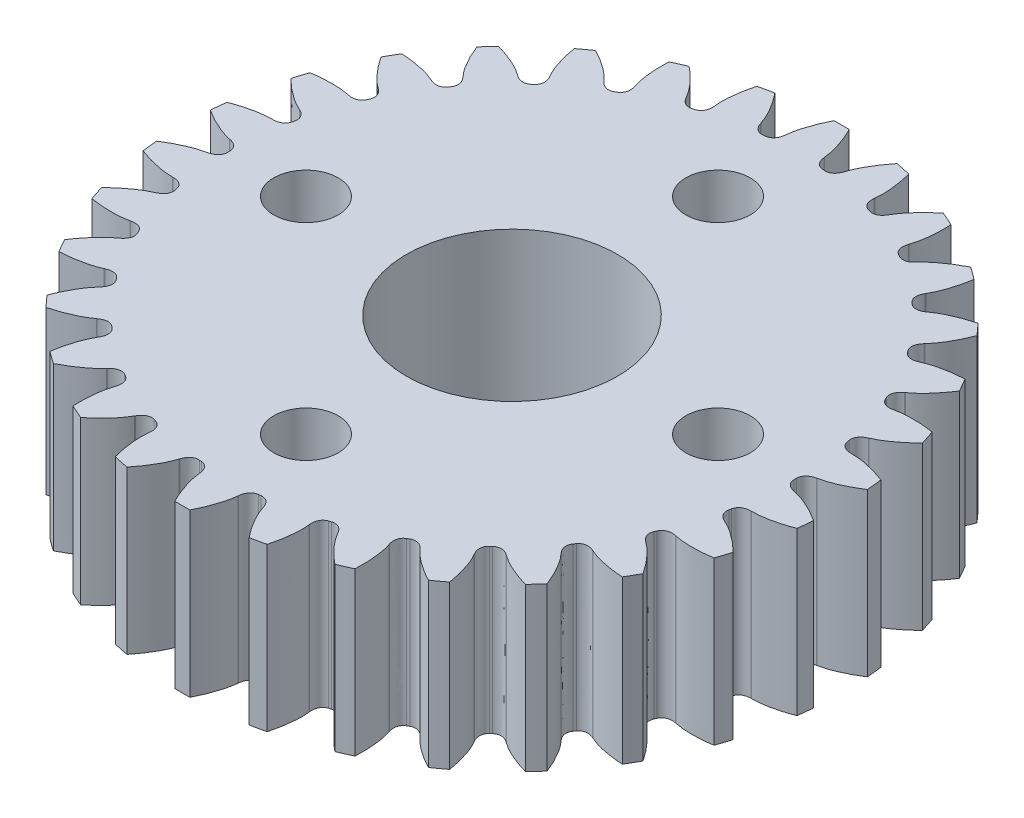
SolidWorks part; units mm, degrees
material "Stainless Steel (ferritic)"
ref_plane "Front Plane" through (0, 0, 0) normal (0, 0, 1) x (1, 0, 0)
ref_plane "Top Plane" through (0, 0, 0) normal (0, 1, 0) x (1, 0, 0)
ref_plane "Right Plane" through (0, 0, 0) normal (1, 0, 0) x (0, 0, -1)
sketch "Sketch2" plane through (0, 0, 0) normal (0, 1, 0) x (1, 0, 0)
  line L0 (11.2477, 1.9391) -> (11.2244, 1.9393)
  line L1 (11.0428, 2.7937) -> (11.064, 2.8034)
  line L2 (10.5988, 4.2353) -> (10.5759, 4.2307)
  line L3 (10.2207, 5.0286) -> (10.2394, 5.0425)
  line L4 (9.4866, 6.3463) -> (9.4652, 6.3371)
  line L5 (8.9518, 7.0437) -> (8.9672, 7.0612)
  line L6 (7.9598, 8.18) -> (7.9408, 8.1665)
  line L7 (7.2917, 8.751) -> (7.3032, 8.7712)
  line L8 (6.0851, 9.6562) -> (6.0694, 9.6391)
  line L9 (5.313, 10.0758) -> (5.32, 10.098)
  line L10 (3.9445, 10.7104) -> (3.9327, 10.6903)
  line L11 (3.102, 10.9602) -> (3.1042, 10.9834)
  line L12 (1.6315, 11.2964) -> (1.6241, 11.2744)
  line L13 (0.7555, 11.3657) -> (0.7528, 11.3888)
  line L14 (-0.7528, 11.3888) -> (-0.7555, 11.3657)
  line L15 (-1.6241, 11.2744) -> (-1.6315, 11.2964)
  line L16 (-3.1042, 10.9834) -> (-3.102, 10.9602)
  line L17 (-3.9327, 10.6903) -> (-3.9445, 10.7104)
  line L18 (-5.32, 10.098) -> (-5.313, 10.0758)
  line L19 (-6.0694, 9.6391) -> (-6.0851, 9.6562)
  line L20 (-7.3032, 8.7712) -> (-7.2917, 8.751)
  line L21 (-7.9408, 8.1665) -> (-7.9598, 8.18)
  line L22 (-8.9672, 7.0612) -> (-8.9518, 7.0437)
  line L23 (-9.4652, 6.3371) -> (-9.4866, 6.3463)
  line L24 (-10.2394, 5.0425) -> (-10.2207, 5.0286)
  line L25 (-10.5759, 4.2307) -> (-10.5988, 4.2353)
  line L26 (-11.064, 2.8034) -> (-11.0428, 2.7937)
  line L27 (-11.2244, 1.9393) -> (-11.2477, 1.9391)
  line L28 (-11.4051, 0.4418) -> (-11.3824, 0.4367)
  line L29 (-11.3824, -0.4367) -> (-11.4051, -0.4418)
  line L30 (-11.2477, -1.9391) -> (-11.2244, -1.9393)
  line L31 (-11.0428, -2.7937) -> (-11.064, -2.8034)
  line L32 (-10.5988, -4.2353) -> (-10.5759, -4.2307)
  line L33 (-10.2207, -5.0286) -> (-10.2394, -5.0425)
  line L34 (-9.4866, -6.3463) -> (-9.4652, -6.3371)
  line L35 (-8.9518, -7.0437) -> (-8.9672, -7.0612)
  line L36 (-7.9598, -8.18) -> (-7.9408, -8.1665)
  line L37 (-7.2917, -8.751) -> (-7.3032, -8.7712)
  line L38 (-6.0851, -9.6562) -> (-6.0694, -9.6391)
  line L39 (-5.313, -10.0758) -> (-5.32, -10.098)
  line L40 (-3.9445, -10.7104) -> (-3.9327, -10.6903)
  line L41 (-3.102, -10.9602) -> (-3.1042, -10.9834)
  line L42 (-1.6315, -11.2964) -> (-1.6241, -11.2744)
  line L43 (-0.7555, -11.3657) -> (-0.7528, -11.3888)
  line L44 (0.7528, -11.3888) -> (0.7555, -11.3657)
  line L45 (1.6241, -11.2744) -> (1.6315, -11.2964)
  line L46 (3.1042, -10.9834) -> (3.102, -10.9602)
  line L47 (3.9327, -10.6903) -> (3.9445, -10.7104)
  line L48 (5.32, -10.098) -> (5.313, -10.0758)
  line L49 (6.0694, -9.6391) -> (6.0851, -9.6562)
  line L50 (7.3032, -8.7712) -> (7.2917, -8.751)
  line L51 (7.9408, -8.1665) -> (7.9598, -8.18)
  line L52 (8.9672, -7.0612) -> (8.9518, -7.0437)
  line L53 (9.4652, -6.3371) -> (9.4866, -6.3463)
  line L54 (10.2394, -5.0425) -> (10.2207, -5.0286)
  line L55 (10.5759, -4.2307) -> (10.5988, -4.2353)
  line L56 (11.064, -2.8034) -> (11.0428, -2.7937)
  line L57 (11.2244, -1.9393) -> (11.2477, -1.9391)
  line L58 (11.4051, -0.4418) -> (11.3824, -0.4367)
  line L59 (11.3824, 0.4367) -> (11.4051, 0.4418)
  arc A0 (12.7573, 1.0443) -> (12.6957, 1.6309) centre (0, 0) ccw
  arc A1 (10.7693, 2.2408) -> (10.7497, 2.3332) centre (0, 0) ccw
  arc A2 (12.2614, 3.6739) -> (12.0792, 4.2349) centre (0, 0) ccw
  arc A3 (10.0681, 4.4309) -> (10.0297, 4.5172) centre (0, 0) ccw
  arc A4 (11.2296, 6.1429) -> (10.9347, 6.6537) centre (0, 0) ccw
  arc A5 (8.9268, 6.4274) -> (8.8714, 6.5038) centre (0, 0) ccw
  arc A6 (9.7071, 8.3434) -> (9.3124, 8.7818) centre (0, 0) ccw
  arc A7 (7.3954, 8.1429) -> (7.3253, 8.2061) centre (0, 0) ccw
  arc A8 (7.7603, 10.1793) -> (7.283, 10.526) centre (0, 0) ccw
  arc A9 (5.5408, 9.5026) -> (5.4591, 9.5498) centre (0, 0) ccw
  arc A10 (5.4743, 11.5703) -> (4.9354, 11.8102) centre (0, 0) ccw
  arc A11 (3.444, 10.4469) -> (3.3543, 10.4761) centre (0, 0) ccw
  arc A12 (2.9491, 12.4556) -> (2.3721, 12.5783) centre (0, 0) ccw
  arc A13 (1.1967, 10.9347) -> (1.1029, 10.9446) centre (0, 0) ccw
  arc A14 (0.2949, 12.7966) -> (-0.2949, 12.7966) centre (0, 0) ccw
  arc A15 (-1.1029, 10.9446) -> (-1.1967, 10.9347) centre (0, 0) ccw
  arc A16 (-2.3721, 12.5783) -> (-2.9491, 12.4556) centre (0, 0) ccw
  arc A17 (-3.3543, 10.4761) -> (-3.444, 10.4469) centre (0, 0) ccw
  arc A18 (-4.9354, 11.8102) -> (-5.4743, 11.5703) centre (0, 0) ccw
  arc A19 (-5.4591, 9.5498) -> (-5.5408, 9.5026) centre (0, 0) ccw
  arc A20 (-7.283, 10.526) -> (-7.7603, 10.1793) centre (0, 0) ccw
  arc A21 (-7.3253, 8.2061) -> (-7.3954, 8.1429) centre (0, 0) ccw
  arc A22 (-9.3124, 8.7818) -> (-9.7071, 8.3434) centre (0, 0) ccw
  arc A23 (-8.8714, 6.5038) -> (-8.9268, 6.4274) centre (0, 0) ccw
  arc A24 (-10.9347, 6.6537) -> (-11.2296, 6.1429) centre (0, 0) ccw
  arc A25 (-10.0297, 4.5172) -> (-10.0681, 4.4309) centre (0, 0) ccw
  arc A26 (-12.0792, 4.2349) -> (-12.2614, 3.6739) centre (0, 0) ccw
  arc A27 (-10.7497, 2.3332) -> (-10.7693, 2.2408) centre (0, 0) ccw
  arc A28 (-12.6957, 1.6309) -> (-12.7573, 1.0443) centre (0, 0) ccw
  arc A29 (-10.9999, 0.0472) -> (-10.9999, -0.0472) centre (0, 0) ccw
  arc A30 (-12.7573, -1.0443) -> (-12.6957, -1.6309) centre (0, 0) ccw
  arc A31 (-10.7693, -2.2408) -> (-10.7497, -2.3332) centre (0, 0) ccw
  arc A32 (-12.2614, -3.6739) -> (-12.0792, -4.2349) centre (0, 0) ccw
  arc A33 (-10.0681, -4.4309) -> (-10.0297, -4.5172) centre (0, 0) ccw
  arc A34 (-11.2296, -6.1429) -> (-10.9347, -6.6537) centre (0, 0) ccw
  arc A35 (-8.9268, -6.4274) -> (-8.8714, -6.5038) centre (0, 0) ccw
  arc A36 (-9.7071, -8.3434) -> (-9.3124, -8.7818) centre (0, 0) ccw
  arc A37 (-7.3954, -8.1429) -> (-7.3253, -8.2061) centre (0, 0) ccw
  arc A38 (-7.7603, -10.1793) -> (-7.283, -10.526) centre (0, 0) ccw
  arc A39 (-5.5408, -9.5026) -> (-5.4591, -9.5498) centre (0, 0) ccw
  arc A40 (-5.4743, -11.5703) -> (-4.9354, -11.8102) centre (0, 0) ccw
  arc A41 (-3.444, -10.4469) -> (-3.3543, -10.4761) centre (0, 0) ccw
  arc A42 (-2.9491, -12.4556) -> (-2.3721, -12.5783) centre (0, 0) ccw
  arc A43 (-1.1967, -10.9347) -> (-1.1029, -10.9446) centre (0, 0) ccw
  arc A44 (-0.2949, -12.7966) -> (0.2949, -12.7966) centre (0, 0) ccw
  arc A45 (1.1029, -10.9446) -> (1.1967, -10.9347) centre (0, 0) ccw
  arc A46 (2.3721, -12.5783) -> (2.9491, -12.4556) centre (0, 0) ccw
  arc A47 (3.3543, -10.4761) -> (3.444, -10.4469) centre (0, 0) ccw
  arc A48 (4.9354, -11.8102) -> (5.4743, -11.5703) centre (0, 0) ccw
  arc A49 (5.4591, -9.5498) -> (5.5408, -9.5026) centre (0, 0) ccw
  arc A50 (7.283, -10.526) -> (7.7603, -10.1793) centre (0, 0) ccw
  arc A51 (7.3253, -8.2061) -> (7.3954, -8.1429) centre (0, 0) ccw
  arc A52 (9.3124, -8.7818) -> (9.7071, -8.3434) centre (0, 0) ccw
  arc A53 (8.8714, -6.5038) -> (8.9268, -6.4274) centre (0, 0) ccw
  arc A54 (10.9347, -6.6537) -> (11.2296, -6.1429) centre (0, 0) ccw
  arc A55 (10.0297, -4.5172) -> (10.0681, -4.4309) centre (0, 0) ccw
  arc A56 (12.0792, -4.2349) -> (12.2614, -3.6739) centre (0, 0) ccw
  arc A57 (10.7497, -2.3332) -> (10.7693, -2.2408) centre (0, 0) ccw
  arc A58 (12.6957, -1.6309) -> (12.7573, -1.0443) centre (0, 0) ccw
  arc A59 (10.9999, -0.0472) -> (10.9999, 0.0472) centre (0, 0) ccw
  spline S0 degree 3 poles (11.2477, 1.9391) (11.3199, 1.9402) (11.4408, 1.9352) (11.6177, 1.9166) (11.7868, 1.8908) (11.979, 1.8522) (12.1936, 1.7985) (12.4359, 1.7256) (12.6049, 1.6656) (12.6957, 1.6309) knots 0 0 0 0 0.000217 0.000362 0.000533 0.000729 0.00095 0.001196 0.001488 0.001488 0.001488 0.001488
  spline S1 degree 3 poles (11.2244, 1.9393) (11.2014, 1.9391) (11.1629, 1.9411) (11.1089, 1.9479) (11.0618, 1.9575) (11.0126, 1.9722) (10.9605, 1.9945) (10.9048, 2.0282) (10.8236, 2.1004) (10.7817, 2.18) (10.7693, 2.2408) knots 0 0 0 0 0.000069 0.000115 0.000162 0.000212 0.000267 0.000331 0.000405 0.000589 0.000589 0.000589 0.000589
  spline S2 degree 3 poles (10.7497, 2.3332) (10.7363, 2.3938) (10.7421, 2.4836) (10.787, 2.5825) (10.8241, 2.636) (10.8627, 2.6775) (10.9016, 2.711) (10.9408, 2.7389) (10.9873, 2.767) (11.0216, 2.7846) (11.0428, 2.7937) knots 0 0 0 0 0.000185 0.000259 0.000323 0.000378 0.000429 0.000476 0.000522 0.000591 0.000591 0.000591 0.000591
  spline S3 degree 3 poles (11.064, 2.8034) (11.1304, 2.8318) (11.2388, 2.8855) (11.3928, 2.9744) (11.5368, 3.0667) (11.6968, 3.1802) (11.8709, 3.3165) (12.0626, 3.4817) (12.1926, 3.6052) (12.2614, 3.6739) knots 0 0 0 0 0.000217 0.000362 0.000533 0.000729 0.00095 0.001196 0.001488 0.001488 0.001488 0.001488
  spline S4 degree 3 poles (12.0792, 4.2349) (11.9831, 4.2499) (11.8054, 4.2735) (11.5532, 4.2944) (11.3322, 4.3023) (11.1361, 4.3001) (10.9653, 4.2902) (10.7884, 4.2715) (10.6692, 4.2513) (10.5988, 4.2353) knots 0 0 0 0 0.000292 0.000538 0.00076 0.000956 0.001127 0.001273 0.00149 0.00149 0.00149 0.00149
  spline S5 degree 3 poles (10.5759, 4.2307) (10.5534, 4.2256) (10.5153, 4.2196) (10.4612, 4.215) (10.4131, 4.2146) (10.3619, 4.2188) (10.3063, 4.2297) (10.2449, 4.2511) (10.1504, 4.3048) (10.0928, 4.374) (10.0681, 4.4309) knots 0 0 0 0 0.000069 0.000115 0.000162 0.000212 0.000267 0.000331 0.000405 0.000589 0.000589 0.000589 0.000589
  spline S6 degree 3 poles (10.0297, 4.5172) (10.004, 4.5737) (9.991, 4.6627) (10.0144, 4.7689) (10.0395, 4.8288) (10.0687, 4.8775) (10.0997, 4.9183) (10.1322, 4.9538) (10.1719, 4.991) (10.2019, 5.0152) (10.2207, 5.0286) knots 0 0 0 0 0.000185 0.000259 0.000323 0.000378 0.000429 0.000476 0.000522 0.000591 0.000591 0.000591 0.000591
  spline S7 degree 3 poles (10.2394, 5.0425) (10.2984, 5.0841) (10.3932, 5.1591) (10.5255, 5.2781) (10.6471, 5.3984) (10.7799, 5.5426) (10.922, 5.7122) (11.0752, 5.9136) (11.1766, 6.0614) (11.2296, 6.1429) knots 0 0 0 0 0.000217 0.000362 0.000533 0.000729 0.00095 0.001196 0.001488 0.001488 0.001488 0.001488
  spline S8 degree 3 poles (10.9347, 6.6537) (10.8377, 6.6485) (10.6589, 6.6346) (10.4079, 6.6026) (10.19, 6.5644) (9.9987, 6.5215) (9.8337, 6.4763) (9.6646, 6.4212) (9.5521, 6.3766) (9.4866, 6.3463) knots 0 0 0 0 0.000292 0.000538 0.00076 0.000956 0.001127 0.001273 0.00149 0.00149 0.00149 0.00149
  spline S9 degree 3 poles (9.4652, 6.3371) (9.4442, 6.3274) (9.4083, 6.3137) (9.3562, 6.2979) (9.3092, 6.2875) (9.2584, 6.281) (9.2017, 6.2801) (9.1371, 6.2883) (9.0335, 6.3211) (8.9629, 6.3769) (8.9268, 6.4274) knots 0 0 0 0 0.000069 0.000115 0.000162 0.000212 0.000267 0.000331 0.000405 0.000589 0.000589 0.000589 0.000589
  spline S10 degree 3 poles (8.8714, 6.5038) (8.8344, 6.5537) (8.8033, 6.6381) (8.804, 6.7468) (8.8162, 6.8106) (8.8345, 6.8643) (8.8565, 6.9107) (8.8809, 6.9521) (8.912, 6.9968) (8.9362, 7.0267) (8.9518, 7.0437) knots 0 0 0 0 0.000185 0.000259 0.000323 0.000378 0.000429 0.000476 0.000522 0.000591 0.000591 0.000591 0.000591
  spline S11 degree 3 poles (8.9672, 7.0612) (9.0163, 7.1141) (9.0935, 7.2073) (9.1981, 7.3511) (9.2921, 7.494) (9.392, 7.6628) (9.4957, 7.8582) (9.6036, 8.087) (9.6721, 8.2527) (9.7071, 8.3434) knots 0 0 0 0 0.000217 0.000362 0.000533 0.000729 0.00095 0.001196 0.001488 0.001488 0.001488 0.001488
  spline S12 degree 3 poles (9.3124, 8.7818) (9.2185, 8.7565) (9.0466, 8.7057) (8.8077, 8.6223) (8.6025, 8.5396) (8.4243, 8.4578) (8.2723, 8.3793) (8.1183, 8.2903) (8.0176, 8.2233) (7.9598, 8.18) knots 0 0 0 0 0.000292 0.000538 0.00076 0.000956 0.001127 0.001273 0.00149 0.00149 0.00149 0.00149
  spline S13 degree 3 poles (7.9408, 8.1665) (7.9223, 8.1527) (7.89, 8.1318) (7.8424, 8.1055) (7.7986, 8.0856) (7.7502, 8.0686) (7.6949, 8.056) (7.6301, 8.0506) (7.5219, 8.0612) (7.4412, 8.101) (7.3954, 8.1429) knots 0 0 0 0 0.000069 0.000115 0.000162 0.000212 0.000267 0.000331 0.000405 0.000589 0.000589 0.000589 0.000589
  spline S14 degree 3 poles (7.3253, 8.2061) (7.2788, 8.2472) (7.2308, 8.3233) (7.2089, 8.4298) (7.2075, 8.4948) (7.2143, 8.5511) (7.2261, 8.601) (7.2414, 8.6467) (7.2625, 8.6968) (7.28, 8.7311) (7.2917, 8.751) knots 0 0 0 0 0.000185 0.000259 0.000323 0.000378 0.000429 0.000476 0.000522 0.000591 0.000591 0.000591 0.000591
  spline S15 degree 3 poles (7.3032, 8.7712) (7.3402, 8.8333) (7.3963, 8.9404) (7.4687, 9.1029) (7.5309, 9.2622) (7.5936, 9.448) (7.6544, 9.6607) (7.7124, 9.907) (7.7449, 10.0833) (7.7603, 10.1793) knots 0 0 0 0 0.000217 0.000362 0.000533 0.000729 0.00095 0.001196 0.001488 0.001488 0.001488 0.001488
  spline S16 degree 3 poles (7.283, 10.526) (7.1965, 10.4818) (7.0389, 10.3963) (6.8225, 10.2651) (6.6391, 10.1415) (6.4817, 10.0245) (6.3494, 9.9161) (6.2173, 9.797) (6.1327, 9.7106) (6.0851, 9.6562) knots 0 0 0 0 0.000292 0.000538 0.00076 0.000956 0.001127 0.001273 0.00149 0.00149 0.00149 0.00149
  spline S17 degree 3 poles (6.0694, 9.6391) (6.0541, 9.6217) (6.0269, 9.5945) (5.9857, 9.5589) (5.9471, 9.5303) (5.9033, 9.5037) (5.8518, 9.4798) (5.7895, 9.461) (5.6815, 9.4489) (5.5943, 9.4711) (5.5408, 9.5026) knots 0 0 0 0 0.000069 0.000115 0.000162 0.000212 0.000267 0.000331 0.000405 0.000589 0.000589 0.000589 0.000589
  spline S18 degree 3 poles (5.4591, 9.5498) (5.405, 9.5804) (5.3422, 9.6448) (5.2987, 9.7444) (5.2838, 9.8077) (5.2788, 9.8642) (5.28, 9.9155) (5.2854, 9.9633) (5.2956, 10.0167) (5.3056, 10.0539) (5.313, 10.0758) knots 0 0 0 0 0.000185 0.000259 0.000323 0.000378 0.000429 0.000476 0.000522 0.000591 0.000591 0.000591 0.000591
  spline S19 degree 3 poles (5.32, 10.098) (5.3432, 10.1664) (5.3758, 10.2828) (5.4129, 10.4568) (5.4406, 10.6256) (5.4633, 10.8204) (5.4785, 11.041) (5.4841, 11.294) (5.4792, 11.4732) (5.4743, 11.5703) knots 0 0 0 0 0.000217 0.000362 0.000533 0.000729 0.00095 0.001196 0.001488 0.001488 0.001488 0.001488
  spline S20 degree 3 poles (4.9354, 11.8102) (4.86, 11.749) (4.7235, 11.6326) (4.5392, 11.4592) (4.3854, 11.3003) (4.2559, 11.1531) (4.149, 11.0195) (4.0445, 10.8756) (3.9797, 10.7734) (3.9445, 10.7104) knots 0 0 0 0 0.000292 0.000538 0.00076 0.000956 0.001127 0.001273 0.00149 0.00149 0.00149 0.00149
  spline S21 degree 3 poles (3.9327, 10.6903) (3.9214, 10.6702) (3.9004, 10.6379) (3.8675, 10.5946) (3.8356, 10.5585) (3.7983, 10.5233) (3.753, 10.4893) (3.696, 10.458) (3.5928, 10.4237) (3.5029, 10.4272) (3.444, 10.4469) knots 0 0 0 0 0.000069 0.000115 0.000162 0.000212 0.000267 0.000331 0.000405 0.000589 0.000589 0.000589 0.000589
  spline S22 degree 3 poles (3.3543, 10.4761) (3.2951, 10.4948) (3.2202, 10.5447) (3.157, 10.6331) (3.1292, 10.6919) (3.1125, 10.7462) (3.103, 10.7966) (3.0984, 10.8444) (3.0973, 10.8988) (3.0993, 10.9373) (3.102, 10.9602) knots 0 0 0 0 0.000185 0.000259 0.000323 0.000378 0.000429 0.000476 0.000522 0.000591 0.000591 0.000591 0.000591
  spline S23 degree 3 poles (3.1042, 10.9834) (3.1128, 11.0551) (3.1204, 11.1758) (3.1205, 11.3537) (3.1125, 11.5245) (3.0942, 11.7198) (3.0632, 11.9388) (3.0161, 12.1874) (2.9741, 12.3617) (2.9491, 12.4556) knots 0 0 0 0 0.000217 0.000362 0.000533 0.000729 0.00095 0.001196 0.001488 0.001488 0.001488 0.001488
  spline S24 degree 3 poles (2.3721, 12.5783) (2.311, 12.5027) (2.2017, 12.3605) (2.0575, 12.1526) (1.9402, 11.9651) (1.844, 11.7942) (1.7672, 11.6413) (1.6949, 11.4788) (1.6529, 11.3654) (1.6315, 11.2964) knots 0 0 0 0 0.000292 0.000538 0.00076 0.000956 0.001127 0.001273 0.00149 0.00149 0.00149 0.00149
  spline S25 degree 3 poles (1.6241, 11.2744) (1.6172, 11.2523) (1.6034, 11.2164) (1.5803, 11.1671) (1.5566, 11.1253) (1.5274, 11.0831) (1.4901, 11.0403) (1.4408, 10.9979) (1.3471, 10.9429) (1.2584, 10.9277) (1.1967, 10.9347) knots 0 0 0 0 0.000069 0.000115 0.000162 0.000212 0.000267 0.000331 0.000405 0.000589 0.000589 0.000589 0.000589
  spline S26 degree 3 poles (1.1029, 10.9446) (1.0411, 10.9505) (0.9575, 10.9838) (0.8772, 11.0571) (0.8379, 11.1089) (0.8103, 11.1585) (0.7905, 11.2058) (0.776, 11.2517) (0.7637, 11.3046) (0.7576, 11.3427) (0.7555, 11.3657) knots 0 0 0 0 0.000185 0.000259 0.000323 0.000378 0.000429 0.000476 0.000522 0.000591 0.000591 0.000591 0.000591
  spline S27 degree 3 poles (0.7528, 11.3888) (0.7463, 11.4607) (0.7287, 11.5804) (0.6918, 11.7544) (0.6484, 11.9198) (0.5899, 12.107) (0.5141, 12.3148) (0.4163, 12.5482) (0.3389, 12.7099) (0.2949, 12.7966) knots 0 0 0 0 0.000217 0.000362 0.000533 0.000729 0.00095 0.001196 0.001488 0.001488 0.001488 0.001488
  spline S28 degree 3 poles (-0.2949, 12.7966) (-0.3389, 12.7099) (-0.4163, 12.5482) (-0.5141, 12.3148) (-0.5899, 12.107) (-0.6484, 11.9198) (-0.6918, 11.7544) (-0.7287, 11.5804) (-0.7463, 11.4607) (-0.7528, 11.3888) knots 0 0 0 0 0.000292 0.000538 0.00076 0.000956 0.001127 0.001273 0.00149 0.00149 0.00149 0.00149
  spline S29 degree 3 poles (-0.7555, 11.3657) (-0.7576, 11.3427) (-0.7637, 11.3046) (-0.776, 11.2517) (-0.7905, 11.2058) (-0.8103, 11.1585) (-0.8379, 11.1089) (-0.8772, 11.0571) (-0.9575, 10.9838) (-1.0411, 10.9505) (-1.1029, 10.9446) knots 0 0 0 0 0.000069 0.000115 0.000162 0.000212 0.000267 0.000331 0.000405 0.000589 0.000589 0.000589 0.000589
  spline S30 degree 3 poles (-1.1967, 10.9347) (-1.2584, 10.9277) (-1.3471, 10.9429) (-1.4408, 10.9979) (-1.4901, 11.0403) (-1.5274, 11.0831) (-1.5566, 11.1253) (-1.5803, 11.1671) (-1.6034, 11.2164) (-1.6172, 11.2523) (-1.6241, 11.2744) knots 0 0 0 0 0.000185 0.000259 0.000323 0.000378 0.000429 0.000476 0.000522 0.000591 0.000591 0.000591 0.000591
  spline S31 degree 3 poles (-1.6315, 11.2964) (-1.6529, 11.3654) (-1.6949, 11.4788) (-1.7672, 11.6413) (-1.844, 11.7942) (-1.9402, 11.9651) (-2.0575, 12.1526) (-2.2017, 12.3605) (-2.311, 12.5027) (-2.3721, 12.5783) knots 0 0 0 0 0.000217 0.000362 0.000533 0.000729 0.00095 0.001196 0.001488 0.001488 0.001488 0.001488
  spline S32 degree 3 poles (-2.9491, 12.4556) (-2.9741, 12.3617) (-3.0161, 12.1874) (-3.0632, 11.9388) (-3.0942, 11.7198) (-3.1125, 11.5245) (-3.1205, 11.3537) (-3.1204, 11.1758) (-3.1128, 11.0551) (-3.1042, 10.9834) knots 0 0 0 0 0.000292 0.000538 0.00076 0.000956 0.001127 0.001273 0.00149 0.00149 0.00149 0.00149
  spline S33 degree 3 poles (-3.102, 10.9602) (-3.0993, 10.9373) (-3.0973, 10.8988) (-3.0984, 10.8444) (-3.103, 10.7966) (-3.1125, 10.7462) (-3.1292, 10.6919) (-3.157, 10.6331) (-3.2202, 10.5447) (-3.2951, 10.4948) (-3.3543, 10.4761) knots 0 0 0 0 0.000069 0.000115 0.000162 0.000212 0.000267 0.000331 0.000405 0.000589 0.000589 0.000589 0.000589
  spline S34 degree 3 poles (-3.444, 10.4469) (-3.5029, 10.4272) (-3.5928, 10.4237) (-3.696, 10.458) (-3.753, 10.4893) (-3.7983, 10.5233) (-3.8356, 10.5585) (-3.8675, 10.5946) (-3.9004, 10.6379) (-3.9214, 10.6702) (-3.9327, 10.6903) knots 0 0 0 0 0.000185 0.000259 0.000323 0.000378 0.000429 0.000476 0.000522 0.000591 0.000591 0.000591 0.000591
  spline S35 degree 3 poles (-3.9445, 10.7104) (-3.9797, 10.7734) (-4.0445, 10.8756) (-4.149, 11.0195) (-4.2559, 11.1531) (-4.3854, 11.3003) (-4.5392, 11.4592) (-4.7235, 11.6326) (-4.86, 11.749) (-4.9354, 11.8102) knots 0 0 0 0 0.000217 0.000362 0.000533 0.000729 0.00095 0.001196 0.001488 0.001488 0.001488 0.001488
  spline S36 degree 3 poles (-5.4743, 11.5703) (-5.4792, 11.4732) (-5.4841, 11.294) (-5.4785, 11.041) (-5.4633, 10.8204) (-5.4406, 10.6256) (-5.4129, 10.4568) (-5.3758, 10.2828) (-5.3432, 10.1664) (-5.32, 10.098) knots 0 0 0 0 0.000292 0.000538 0.00076 0.000956 0.001127 0.001273 0.00149 0.00149 0.00149 0.00149
  spline S37 degree 3 poles (-5.313, 10.0758) (-5.3056, 10.0539) (-5.2956, 10.0167) (-5.2854, 9.9633) (-5.28, 9.9155) (-5.2788, 9.8642) (-5.2838, 9.8077) (-5.2987, 9.7444) (-5.3422, 9.6448) (-5.405, 9.5804) (-5.4591, 9.5498) knots 0 0 0 0 0.000069 0.000115 0.000162 0.000212 0.000267 0.000331 0.000405 0.000589 0.000589 0.000589 0.000589
  spline S38 degree 3 poles (-5.5408, 9.5026) (-5.5943, 9.4711) (-5.6815, 9.4489) (-5.7895, 9.461) (-5.8518, 9.4798) (-5.9033, 9.5037) (-5.9471, 9.5303) (-5.9857, 9.5589) (-6.0269, 9.5945) (-6.0541, 9.6217) (-6.0694, 9.6391) knots 0 0 0 0 0.000185 0.000259 0.000323 0.000378 0.000429 0.000476 0.000522 0.000591 0.000591 0.000591 0.000591
  spline S39 degree 3 poles (-6.0851, 9.6562) (-6.1327, 9.7106) (-6.2173, 9.797) (-6.3494, 9.9161) (-6.4817, 10.0245) (-6.6391, 10.1415) (-6.8225, 10.2651) (-7.0389, 10.3963) (-7.1965, 10.4818) (-7.283, 10.526) knots 0 0 0 0 0.000217 0.000362 0.000533 0.000729 0.00095 0.001196 0.001488 0.001488 0.001488 0.001488
  spline S40 degree 3 poles (-7.7603, 10.1793) (-7.7449, 10.0833) (-7.7124, 9.907) (-7.6544, 9.6607) (-7.5936, 9.448) (-7.5309, 9.2622) (-7.4687, 9.1029) (-7.3963, 8.9404) (-7.3402, 8.8333) (-7.3032, 8.7712) knots 0 0 0 0 0.000292 0.000538 0.00076 0.000956 0.001127 0.001273 0.00149 0.00149 0.00149 0.00149
  spline S41 degree 3 poles (-7.2917, 8.751) (-7.28, 8.7311) (-7.2625, 8.6968) (-7.2414, 8.6467) (-7.2261, 8.601) (-7.2143, 8.5511) (-7.2075, 8.4948) (-7.2089, 8.4298) (-7.2308, 8.3233) (-7.2788, 8.2472) (-7.3253, 8.2061) knots 0 0 0 0 0.000069 0.000115 0.000162 0.000212 0.000267 0.000331 0.000405 0.000589 0.000589 0.000589 0.000589
  spline S42 degree 3 poles (-7.3954, 8.1429) (-7.4412, 8.101) (-7.5219, 8.0612) (-7.6301, 8.0506) (-7.6949, 8.056) (-7.7502, 8.0686) (-7.7986, 8.0856) (-7.8424, 8.1055) (-7.89, 8.1318) (-7.9223, 8.1527) (-7.9408, 8.1665) knots 0 0 0 0 0.000185 0.000259 0.000323 0.000378 0.000429 0.000476 0.000522 0.000591 0.000591 0.000591 0.000591
  spline S43 degree 3 poles (-7.9598, 8.18) (-8.0176, 8.2233) (-8.1183, 8.2903) (-8.2723, 8.3793) (-8.4243, 8.4578) (-8.6025, 8.5396) (-8.8077, 8.6223) (-9.0466, 8.7057) (-9.2185, 8.7565) (-9.3124, 8.7818) knots 0 0 0 0 0.000217 0.000362 0.000533 0.000729 0.00095 0.001196 0.001488 0.001488 0.001488 0.001488
  spline S44 degree 3 poles (-9.7071, 8.3434) (-9.6721, 8.2527) (-9.6036, 8.087) (-9.4957, 7.8582) (-9.392, 7.6628) (-9.2921, 7.494) (-9.1981, 7.3511) (-9.0935, 7.2073) (-9.0163, 7.1141) (-8.9672, 7.0612) knots 0 0 0 0 0.000292 0.000538 0.00076 0.000956 0.001127 0.001273 0.00149 0.00149 0.00149 0.00149
  spline S45 degree 3 poles (-8.9518, 7.0437) (-8.9362, 7.0267) (-8.912, 6.9968) (-8.8809, 6.9521) (-8.8565, 6.9107) (-8.8345, 6.8643) (-8.8162, 6.8106) (-8.804, 6.7468) (-8.8033, 6.6381) (-8.8344, 6.5537) (-8.8714, 6.5038) knots 0 0 0 0 0.000069 0.000115 0.000162 0.000212 0.000267 0.000331 0.000405 0.000589 0.000589 0.000589 0.000589
  spline S46 degree 3 poles (-8.9268, 6.4274) (-8.9629, 6.3769) (-9.0335, 6.3211) (-9.1371, 6.2883) (-9.2017, 6.2801) (-9.2584, 6.281) (-9.3092, 6.2875) (-9.3562, 6.2979) (-9.4083, 6.3137) (-9.4442, 6.3274) (-9.4652, 6.3371) knots 0 0 0 0 0.000185 0.000259 0.000323 0.000378 0.000429 0.000476 0.000522 0.000591 0.000591 0.000591 0.000591
  spline S47 degree 3 poles (-9.4866, 6.3463) (-9.5521, 6.3766) (-9.6646, 6.4212) (-9.8337, 6.4763) (-9.9987, 6.5215) (-10.19, 6.5644) (-10.4079, 6.6026) (-10.6589, 6.6346) (-10.8377, 6.6485) (-10.9347, 6.6537) knots 0 0 0 0 0.000217 0.000362 0.000533 0.000729 0.00095 0.001196 0.001488 0.001488 0.001488 0.001488
  spline S48 degree 3 poles (-11.2296, 6.1429) (-11.1766, 6.0614) (-11.0752, 5.9136) (-10.922, 5.7122) (-10.7799, 5.5426) (-10.6471, 5.3984) (-10.5255, 5.2781) (-10.3932, 5.1591) (-10.2984, 5.0841) (-10.2394, 5.0425) knots 0 0 0 0 0.000292 0.000538 0.00076 0.000956 0.001127 0.001273 0.00149 0.00149 0.00149 0.00149
  spline S49 degree 3 poles (-10.2207, 5.0286) (-10.2019, 5.0152) (-10.1719, 4.991) (-10.1322, 4.9538) (-10.0997, 4.9183) (-10.0687, 4.8775) (-10.0395, 4.8288) (-10.0144, 4.7689) (-9.991, 4.6627) (-10.004, 4.5737) (-10.0297, 4.5172) knots 0 0 0 0 0.000069 0.000115 0.000162 0.000212 0.000267 0.000331 0.000405 0.000589 0.000589 0.000589 0.000589
  spline S50 degree 3 poles (-10.0681, 4.4309) (-10.0928, 4.374) (-10.1504, 4.3048) (-10.2449, 4.2511) (-10.3063, 4.2297) (-10.3619, 4.2188) (-10.4131, 4.2146) (-10.4612, 4.215) (-10.5153, 4.2196) (-10.5534, 4.2256) (-10.5759, 4.2307) knots 0 0 0 0 0.000185 0.000259 0.000323 0.000378 0.000429 0.000476 0.000522 0.000591 0.000591 0.000591 0.000591
  spline S51 degree 3 poles (-10.5988, 4.2353) (-10.6692, 4.2513) (-10.7884, 4.2715) (-10.9653, 4.2902) (-11.1361, 4.3001) (-11.3322, 4.3023) (-11.5532, 4.2944) (-11.8054, 4.2735) (-11.9831, 4.2499) (-12.0792, 4.2349) knots 0 0 0 0 0.000217 0.000362 0.000533 0.000729 0.00095 0.001196 0.001488 0.001488 0.001488 0.001488
  spline S52 degree 3 poles (-12.2614, 3.6739) (-12.1926, 3.6052) (-12.0626, 3.4817) (-11.8709, 3.3165) (-11.6968, 3.1802) (-11.5368, 3.0667) (-11.3928, 2.9744) (-11.2388, 2.8855) (-11.1304, 2.8318) (-11.064, 2.8034) knots 0 0 0 0 0.000292 0.000538 0.00076 0.000956 0.001127 0.001273 0.00149 0.00149 0.00149 0.00149
  spline S53 degree 3 poles (-11.0428, 2.7937) (-11.0216, 2.7846) (-10.9873, 2.767) (-10.9408, 2.7389) (-10.9016, 2.711) (-10.8627, 2.6775) (-10.8241, 2.636) (-10.787, 2.5825) (-10.7421, 2.4836) (-10.7363, 2.3938) (-10.7497, 2.3332) knots 0 0 0 0 0.000069 0.000115 0.000162 0.000212 0.000267 0.000331 0.000405 0.000589 0.000589 0.000589 0.000589
  spline S54 degree 3 poles (-10.7693, 2.2408) (-10.7817, 2.18) (-10.8236, 2.1004) (-10.9048, 2.0282) (-10.9605, 1.9945) (-11.0126, 1.9722) (-11.0618, 1.9575) (-11.1089, 1.9479) (-11.1629, 1.9411) (-11.2014, 1.9391) (-11.2244, 1.9393) knots 0 0 0 0 0.000185 0.000259 0.000323 0.000378 0.000429 0.000476 0.000522 0.000591 0.000591 0.000591 0.000591
  spline S55 degree 3 poles (-11.2477, 1.9391) (-11.3199, 1.9402) (-11.4408, 1.9352) (-11.6177, 1.9166) (-11.7868, 1.8908) (-11.979, 1.8522) (-12.1936, 1.7985) (-12.4359, 1.7256) (-12.6049, 1.6656) (-12.6957, 1.6309) knots 0 0 0 0 0.000217 0.000362 0.000533 0.000729 0.00095 0.001196 0.001488 0.001488 0.001488 0.001488
  spline S56 degree 3 poles (-12.7573, 1.0443) (-12.6757, 0.9915) (-12.5229, 0.8977) (-12.3011, 0.776) (-12.1024, 0.6788) (-11.9223, 0.6011) (-11.7623, 0.5407) (-11.5931, 0.4858) (-11.4759, 0.4558) (-11.4051, 0.4418) knots 0 0 0 0 0.000292 0.000538 0.00076 0.000956 0.001127 0.001273 0.00149 0.00149 0.00149 0.00149
  spline S57 degree 3 poles (-11.3824, 0.4367) (-11.3597, 0.4322) (-11.3225, 0.4222) (-11.2711, 0.4043) (-11.227, 0.3851) (-11.182, 0.3605) (-11.1356, 0.3279) (-11.0882, 0.2834) (-11.0238, 0.1959) (-10.9993, 0.1093) (-10.9999, 0.0472) knots 0 0 0 0 0.000069 0.000115 0.000162 0.000212 0.000267 0.000331 0.000405 0.000589 0.000589 0.000589 0.000589
  spline S58 degree 3 poles (-10.9999, -0.0472) (-10.9993, -0.1093) (-11.0238, -0.1959) (-11.0882, -0.2834) (-11.1356, -0.3279) (-11.182, -0.3605) (-11.227, -0.3851) (-11.2711, -0.4043) (-11.3225, -0.4222) (-11.3597, -0.4322) (-11.3824, -0.4367) knots 0 0 0 0 0.000185 0.000259 0.000323 0.000378 0.000429 0.000476 0.000522 0.000591 0.000591 0.000591 0.000591
  spline S59 degree 3 poles (-11.4051, -0.4418) (-11.4759, -0.4558) (-11.5931, -0.4858) (-11.7623, -0.5407) (-11.9223, -0.6011) (-12.1024, -0.6788) (-12.3011, -0.776) (-12.5229, -0.8977) (-12.6757, -0.9915) (-12.7573, -1.0443) knots 0 0 0 0 0.000217 0.000362 0.000533 0.000729 0.00095 0.001196 0.001488 0.001488 0.001488 0.001488
  spline S60 degree 3 poles (-12.6957, -1.6309) (-12.6049, -1.6656) (-12.4359, -1.7256) (-12.1936, -1.7985) (-11.979, -1.8522) (-11.7868, -1.8908) (-11.6177, -1.9166) (-11.4408, -1.9352) (-11.3199, -1.9402) (-11.2477, -1.9391) knots 0 0 0 0 0.000292 0.000538 0.00076 0.000956 0.001127 0.001273 0.00149 0.00149 0.00149 0.00149
  spline S61 degree 3 poles (-11.2244, -1.9393) (-11.2014, -1.9391) (-11.1629, -1.9411) (-11.1089, -1.9479) (-11.0618, -1.9575) (-11.0126, -1.9722) (-10.9605, -1.9945) (-10.9048, -2.0282) (-10.8236, -2.1004) (-10.7817, -2.18) (-10.7693, -2.2408) knots 0 0 0 0 0.000069 0.000115 0.000162 0.000212 0.000267 0.000331 0.000405 0.000589 0.000589 0.000589 0.000589
  spline S62 degree 3 poles (-10.7497, -2.3332) (-10.7363, -2.3938) (-10.7421, -2.4836) (-10.787, -2.5825) (-10.8241, -2.636) (-10.8627, -2.6775) (-10.9016, -2.711) (-10.9408, -2.7389) (-10.9873, -2.767) (-11.0216, -2.7846) (-11.0428, -2.7937) knots 0 0 0 0 0.000185 0.000259 0.000323 0.000378 0.000429 0.000476 0.000522 0.000591 0.000591 0.000591 0.000591
  spline S63 degree 3 poles (-11.064, -2.8034) (-11.1304, -2.8318) (-11.2388, -2.8855) (-11.3928, -2.9744) (-11.5368, -3.0667) (-11.6968, -3.1802) (-11.8709, -3.3165) (-12.0626, -3.4817) (-12.1926, -3.6052) (-12.2614, -3.6739) knots 0 0 0 0 0.000217 0.000362 0.000533 0.000729 0.00095 0.001196 0.001488 0.001488 0.001488 0.001488
  spline S64 degree 3 poles (-12.0792, -4.2349) (-11.9831, -4.2499) (-11.8054, -4.2735) (-11.5532, -4.2944) (-11.3322, -4.3023) (-11.1361, -4.3001) (-10.9653, -4.2902) (-10.7884, -4.2715) (-10.6692, -4.2513) (-10.5988, -4.2353) knots 0 0 0 0 0.000292 0.000538 0.00076 0.000956 0.001127 0.001273 0.00149 0.00149 0.00149 0.00149
  spline S65 degree 3 poles (-10.5759, -4.2307) (-10.5534, -4.2256) (-10.5153, -4.2196) (-10.4612, -4.215) (-10.4131, -4.2146) (-10.3619, -4.2188) (-10.3063, -4.2297) (-10.2449, -4.2511) (-10.1504, -4.3048) (-10.0928, -4.374) (-10.0681, -4.4309) knots 0 0 0 0 0.000069 0.000115 0.000162 0.000212 0.000267 0.000331 0.000405 0.000589 0.000589 0.000589 0.000589
  spline S66 degree 3 poles (-10.0297, -4.5172) (-10.004, -4.5737) (-9.991, -4.6627) (-10.0144, -4.7689) (-10.0395, -4.8288) (-10.0687, -4.8775) (-10.0997, -4.9183) (-10.1322, -4.9538) (-10.1719, -4.991) (-10.2019, -5.0152) (-10.2207, -5.0286) knots 0 0 0 0 0.000185 0.000259 0.000323 0.000378 0.000429 0.000476 0.000522 0.000591 0.000591 0.000591 0.000591
  spline S67 degree 3 poles (-10.2394, -5.0425) (-10.2984, -5.0841) (-10.3932, -5.1591) (-10.5255, -5.2781) (-10.6471, -5.3984) (-10.7799, -5.5426) (-10.922, -5.7122) (-11.0752, -5.9136) (-11.1766, -6.0614) (-11.2296, -6.1429) knots 0 0 0 0 0.000217 0.000362 0.000533 0.000729 0.00095 0.001196 0.001488 0.001488 0.001488 0.001488
  spline S68 degree 3 poles (-10.9347, -6.6537) (-10.8377, -6.6485) (-10.6589, -6.6346) (-10.4079, -6.6026) (-10.19, -6.5644) (-9.9987, -6.5215) (-9.8337, -6.4763) (-9.6646, -6.4212) (-9.5521, -6.3766) (-9.4866, -6.3463) knots 0 0 0 0 0.000292 0.000538 0.00076 0.000956 0.001127 0.001273 0.00149 0.00149 0.00149 0.00149
  spline S69 degree 3 poles (-9.4652, -6.3371) (-9.4442, -6.3274) (-9.4083, -6.3137) (-9.3562, -6.2979) (-9.3092, -6.2875) (-9.2584, -6.281) (-9.2017, -6.2801) (-9.1371, -6.2883) (-9.0335, -6.3211) (-8.9629, -6.3769) (-8.9268, -6.4274) knots 0 0 0 0 0.000069 0.000115 0.000162 0.000212 0.000267 0.000331 0.000405 0.000589 0.000589 0.000589 0.000589
  spline S70 degree 3 poles (-8.8714, -6.5038) (-8.8344, -6.5537) (-8.8033, -6.6381) (-8.804, -6.7468) (-8.8162, -6.8106) (-8.8345, -6.8643) (-8.8565, -6.9107) (-8.8809, -6.9521) (-8.912, -6.9968) (-8.9362, -7.0267) (-8.9518, -7.0437) knots 0 0 0 0 0.000185 0.000259 0.000323 0.000378 0.000429 0.000476 0.000522 0.000591 0.000591 0.000591 0.000591
  spline S71 degree 3 poles (-8.9672, -7.0612) (-9.0163, -7.1141) (-9.0935, -7.2073) (-9.1981, -7.3511) (-9.2921, -7.494) (-9.392, -7.6628) (-9.4957, -7.8582) (-9.6036, -8.087) (-9.6721, -8.2527) (-9.7071, -8.3434) knots 0 0 0 0 0.000217 0.000362 0.000533 0.000729 0.00095 0.001196 0.001488 0.001488 0.001488 0.001488
  spline S72 degree 3 poles (-9.3124, -8.7818) (-9.2185, -8.7565) (-9.0466, -8.7057) (-8.8077, -8.6223) (-8.6025, -8.5396) (-8.4243, -8.4578) (-8.2723, -8.3793) (-8.1183, -8.2903) (-8.0176, -8.2233) (-7.9598, -8.18) knots 0 0 0 0 0.000292 0.000538 0.00076 0.000956 0.001127 0.001273 0.00149 0.00149 0.00149 0.00149
  spline S73 degree 3 poles (-7.9408, -8.1665) (-7.9223, -8.1527) (-7.89, -8.1318) (-7.8424, -8.1055) (-7.7986, -8.0856) (-7.7502, -8.0686) (-7.6949, -8.056) (-7.6301, -8.0506) (-7.5219, -8.0612) (-7.4412, -8.101) (-7.3954, -8.1429) knots 0 0 0 0 0.000069 0.000115 0.000162 0.000212 0.000267 0.000331 0.000405 0.000589 0.000589 0.000589 0.000589
  spline S74 degree 3 poles (-7.3253, -8.2061) (-7.2788, -8.2472) (-7.2308, -8.3233) (-7.2089, -8.4298) (-7.2075, -8.4948) (-7.2143, -8.5511) (-7.2261, -8.601) (-7.2414, -8.6467) (-7.2625, -8.6968) (-7.28, -8.7311) (-7.2917, -8.751) knots 0 0 0 0 0.000185 0.000259 0.000323 0.000378 0.000429 0.000476 0.000522 0.000591 0.000591 0.000591 0.000591
  spline S75 degree 3 poles (-7.3032, -8.7712) (-7.3402, -8.8333) (-7.3963, -8.9404) (-7.4687, -9.1029) (-7.5309, -9.2622) (-7.5936, -9.448) (-7.6544, -9.6607) (-7.7124, -9.907) (-7.7449, -10.0833) (-7.7603, -10.1793) knots 0 0 0 0 0.000217 0.000362 0.000533 0.000729 0.00095 0.001196 0.001488 0.001488 0.001488 0.001488
  spline S76 degree 3 poles (-7.283, -10.526) (-7.1965, -10.4818) (-7.0389, -10.3963) (-6.8225, -10.2651) (-6.6391, -10.1415) (-6.4817, -10.0245) (-6.3494, -9.9161) (-6.2173, -9.797) (-6.1327, -9.7106) (-6.0851, -9.6562) knots 0 0 0 0 0.000292 0.000538 0.00076 0.000956 0.001127 0.001273 0.00149 0.00149 0.00149 0.00149
  spline S77 degree 3 poles (-6.0694, -9.6391) (-6.0541, -9.6217) (-6.0269, -9.5945) (-5.9857, -9.5589) (-5.9471, -9.5303) (-5.9033, -9.5037) (-5.8518, -9.4798) (-5.7895, -9.461) (-5.6815, -9.4489) (-5.5943, -9.4711) (-5.5408, -9.5026) knots 0 0 0 0 0.000069 0.000115 0.000162 0.000212 0.000267 0.000331 0.000405 0.000589 0.000589 0.000589 0.000589
  spline S78 degree 3 poles (-5.4591, -9.5498) (-5.405, -9.5804) (-5.3422, -9.6448) (-5.2987, -9.7444) (-5.2838, -9.8077) (-5.2788, -9.8642) (-5.28, -9.9155) (-5.2854, -9.9633) (-5.2956, -10.0167) (-5.3056, -10.0539) (-5.313, -10.0758) knots 0 0 0 0 0.000185 0.000259 0.000323 0.000378 0.000429 0.000476 0.000522 0.000591 0.000591 0.000591 0.000591
  spline S79 degree 3 poles (-5.32, -10.098) (-5.3432, -10.1664) (-5.3758, -10.2828) (-5.4129, -10.4568) (-5.4406, -10.6256) (-5.4633, -10.8204) (-5.4785, -11.041) (-5.4841, -11.294) (-5.4792, -11.4732) (-5.4743, -11.5703) knots 0 0 0 0 0.000217 0.000362 0.000533 0.000729 0.00095 0.001196 0.001488 0.001488 0.001488 0.001488
  spline S80 degree 3 poles (-4.9354, -11.8102) (-4.86, -11.749) (-4.7235, -11.6326) (-4.5392, -11.4592) (-4.3854, -11.3003) (-4.2559, -11.1531) (-4.149, -11.0195) (-4.0445, -10.8756) (-3.9797, -10.7734) (-3.9445, -10.7104) knots 0 0 0 0 0.000292 0.000538 0.00076 0.000956 0.001127 0.001273 0.00149 0.00149 0.00149 0.00149
  spline S81 degree 3 poles (-3.9327, -10.6903) (-3.9214, -10.6702) (-3.9004, -10.6379) (-3.8675, -10.5946) (-3.8356, -10.5585) (-3.7983, -10.5233) (-3.753, -10.4893) (-3.696, -10.458) (-3.5928, -10.4237) (-3.5029, -10.4272) (-3.444, -10.4469) knots 0 0 0 0 0.000069 0.000115 0.000162 0.000212 0.000267 0.000331 0.000405 0.000589 0.000589 0.000589 0.000589
  spline S82 degree 3 poles (-3.3543, -10.4761) (-3.2951, -10.4948) (-3.2202, -10.5447) (-3.157, -10.6331) (-3.1292, -10.6919) (-3.1125, -10.7462) (-3.103, -10.7966) (-3.0984, -10.8444) (-3.0973, -10.8988) (-3.0993, -10.9373) (-3.102, -10.9602) knots 0 0 0 0 0.000185 0.000259 0.000323 0.000378 0.000429 0.000476 0.000522 0.000591 0.000591 0.000591 0.000591
  spline S83 degree 3 poles (-3.1042, -10.9834) (-3.1128, -11.0551) (-3.1204, -11.1758) (-3.1205, -11.3537) (-3.1125, -11.5245) (-3.0942, -11.7198) (-3.0632, -11.9388) (-3.0161, -12.1874) (-2.9741, -12.3617) (-2.9491, -12.4556) knots 0 0 0 0 0.000217 0.000362 0.000533 0.000729 0.00095 0.001196 0.001488 0.001488 0.001488 0.001488
  spline S84 degree 3 poles (-2.3721, -12.5783) (-2.311, -12.5027) (-2.2017, -12.3605) (-2.0575, -12.1526) (-1.9402, -11.9651) (-1.844, -11.7942) (-1.7672, -11.6413) (-1.6949, -11.4788) (-1.6529, -11.3654) (-1.6315, -11.2964) knots 0 0 0 0 0.000292 0.000538 0.00076 0.000956 0.001127 0.001273 0.00149 0.00149 0.00149 0.00149
  spline S85 degree 3 poles (-1.6241, -11.2744) (-1.6172, -11.2523) (-1.6034, -11.2164) (-1.5803, -11.1671) (-1.5566, -11.1253) (-1.5274, -11.0831) (-1.4901, -11.0403) (-1.4408, -10.9979) (-1.3471, -10.9429) (-1.2584, -10.9277) (-1.1967, -10.9347) knots 0 0 0 0 0.000069 0.000115 0.000162 0.000212 0.000267 0.000331 0.000405 0.000589 0.000589 0.000589 0.000589
  spline S86 degree 3 poles (-1.1029, -10.9446) (-1.0411, -10.9505) (-0.9575, -10.9838) (-0.8772, -11.0571) (-0.8379, -11.1089) (-0.8103, -11.1585) (-0.7905, -11.2058) (-0.776, -11.2517) (-0.7637, -11.3046) (-0.7576, -11.3427) (-0.7555, -11.3657) knots 0 0 0 0 0.000185 0.000259 0.000323 0.000378 0.000429 0.000476 0.000522 0.000591 0.000591 0.000591 0.000591
  spline S87 degree 3 poles (-0.7528, -11.3888) (-0.7463, -11.4607) (-0.7287, -11.5804) (-0.6918, -11.7544) (-0.6484, -11.9198) (-0.5899, -12.107) (-0.5141, -12.3148) (-0.4163, -12.5482) (-0.3389, -12.7099) (-0.2949, -12.7966) knots 0 0 0 0 0.000217 0.000362 0.000533 0.000729 0.00095 0.001196 0.001488 0.001488 0.001488 0.001488
  spline S88 degree 3 poles (0.2949, -12.7966) (0.3389, -12.7099) (0.4163, -12.5482) (0.5141, -12.3148) (0.5899, -12.107) (0.6484, -11.9198) (0.6918, -11.7544) (0.7287, -11.5804) (0.7463, -11.4607) (0.7528, -11.3888) knots 0 0 0 0 0.000292 0.000538 0.00076 0.000956 0.001127 0.001273 0.00149 0.00149 0.00149 0.00149
  spline S89 degree 3 poles (0.7555, -11.3657) (0.7576, -11.3427) (0.7637, -11.3046) (0.776, -11.2517) (0.7905, -11.2058) (0.8103, -11.1585) (0.8379, -11.1089) (0.8772, -11.0571) (0.9575, -10.9838) (1.0411, -10.9505) (1.1029, -10.9446) knots 0 0 0 0 0.000069 0.000115 0.000162 0.000212 0.000267 0.000331 0.000405 0.000589 0.000589 0.000589 0.000589
  spline S90 degree 3 poles (1.1967, -10.9347) (1.2584, -10.9277) (1.3471, -10.9429) (1.4408, -10.9979) (1.4901, -11.0403) (1.5274, -11.0831) (1.5566, -11.1253) (1.5803, -11.1671) (1.6034, -11.2164) (1.6172, -11.2523) (1.6241, -11.2744) knots 0 0 0 0 0.000185 0.000259 0.000323 0.000378 0.000429 0.000476 0.000522 0.000591 0.000591 0.000591 0.000591
  spline S91 degree 3 poles (1.6315, -11.2964) (1.6529, -11.3654) (1.6949, -11.4788) (1.7672, -11.6413) (1.844, -11.7942) (1.9402, -11.9651) (2.0575, -12.1526) (2.2017, -12.3605) (2.311, -12.5027) (2.3721, -12.5783) knots 0 0 0 0 0.000217 0.000362 0.000533 0.000729 0.00095 0.001196 0.001488 0.001488 0.001488 0.001488
  spline S92 degree 3 poles (2.9491, -12.4556) (2.9741, -12.3617) (3.0161, -12.1874) (3.0632, -11.9388) (3.0942, -11.7198) (3.1125, -11.5245) (3.1205, -11.3537) (3.1204, -11.1758) (3.1128, -11.0551) (3.1042, -10.9834) knots 0 0 0 0 0.000292 0.000538 0.00076 0.000956 0.001127 0.001273 0.00149 0.00149 0.00149 0.00149
  spline S93 degree 3 poles (3.102, -10.9602) (3.0993, -10.9373) (3.0973, -10.8988) (3.0984, -10.8444) (3.103, -10.7966) (3.1125, -10.7462) (3.1292, -10.6919) (3.157, -10.6331) (3.2202, -10.5447) (3.2951, -10.4948) (3.3543, -10.4761) knots 0 0 0 0 0.000069 0.000115 0.000162 0.000212 0.000267 0.000331 0.000405 0.000589 0.000589 0.000589 0.000589
  spline S94 degree 3 poles (3.444, -10.4469) (3.5029, -10.4272) (3.5928, -10.4237) (3.696, -10.458) (3.753, -10.4893) (3.7983, -10.5233) (3.8356, -10.5585) (3.8675, -10.5946) (3.9004, -10.6379) (3.9214, -10.6702) (3.9327, -10.6903) knots 0 0 0 0 0.000185 0.000259 0.000323 0.000378 0.000429 0.000476 0.000522 0.000591 0.000591 0.000591 0.000591
  spline S95 degree 3 poles (3.9445, -10.7104) (3.9797, -10.7734) (4.0445, -10.8756) (4.149, -11.0195) (4.2559, -11.1531) (4.3854, -11.3003) (4.5392, -11.4592) (4.7235, -11.6326) (4.86, -11.749) (4.9354, -11.8102) knots 0 0 0 0 0.000217 0.000362 0.000533 0.000729 0.00095 0.001196 0.001488 0.001488 0.001488 0.001488
  spline S96 degree 3 poles (5.4743, -11.5703) (5.4792, -11.4732) (5.4841, -11.294) (5.4785, -11.041) (5.4633, -10.8204) (5.4406, -10.6256) (5.4129, -10.4568) (5.3758, -10.2828) (5.3432, -10.1664) (5.32, -10.098) knots 0 0 0 0 0.000292 0.000538 0.00076 0.000956 0.001127 0.001273 0.00149 0.00149 0.00149 0.00149
  spline S97 degree 3 poles (5.313, -10.0758) (5.3056, -10.0539) (5.2956, -10.0167) (5.2854, -9.9633) (5.28, -9.9155) (5.2788, -9.8642) (5.2838, -9.8077) (5.2987, -9.7444) (5.3422, -9.6448) (5.405, -9.5804) (5.4591, -9.5498) knots 0 0 0 0 0.000069 0.000115 0.000162 0.000212 0.000267 0.000331 0.000405 0.000589 0.000589 0.000589 0.000589
  spline S98 degree 3 poles (5.5408, -9.5026) (5.5943, -9.4711) (5.6815, -9.4489) (5.7895, -9.461) (5.8518, -9.4798) (5.9033, -9.5037) (5.9471, -9.5303) (5.9857, -9.5589) (6.0269, -9.5945) (6.0541, -9.6217) (6.0694, -9.6391) knots 0 0 0 0 0.000185 0.000259 0.000323 0.000378 0.000429 0.000476 0.000522 0.000591 0.000591 0.000591 0.000591
  spline S99 degree 3 poles (6.0851, -9.6562) (6.1327, -9.7106) (6.2173, -9.797) (6.3494, -9.9161) (6.4817, -10.0245) (6.6391, -10.1415) (6.8225, -10.2651) (7.0389, -10.3963) (7.1965, -10.4818) (7.283, -10.526) knots 0 0 0 0 0.000217 0.000362 0.000533 0.000729 0.00095 0.001196 0.001488 0.001488 0.001488 0.001488
  spline S100 degree 3 poles (7.7603, -10.1793) (7.7449, -10.0833) (7.7124, -9.907) (7.6544, -9.6607) (7.5936, -9.448) (7.5309, -9.2622) (7.4687, -9.1029) (7.3963, -8.9404) (7.3402, -8.8333) (7.3032, -8.7712) knots 0 0 0 0 0.000292 0.000538 0.00076 0.000956 0.001127 0.001273 0.00149 0.00149 0.00149 0.00149
  spline S101 degree 3 poles (7.2917, -8.751) (7.28, -8.7311) (7.2625, -8.6968) (7.2414, -8.6467) (7.2261, -8.601) (7.2143, -8.5511) (7.2075, -8.4948) (7.2089, -8.4298) (7.2308, -8.3233) (7.2788, -8.2472) (7.3253, -8.2061) knots 0 0 0 0 0.000069 0.000115 0.000162 0.000212 0.000267 0.000331 0.000405 0.000589 0.000589 0.000589 0.000589
  spline S102 degree 3 poles (7.3954, -8.1429) (7.4412, -8.101) (7.5219, -8.0612) (7.6301, -8.0506) (7.6949, -8.056) (7.7502, -8.0686) (7.7986, -8.0856) (7.8424, -8.1055) (7.89, -8.1318) (7.9223, -8.1527) (7.9408, -8.1665) knots 0 0 0 0 0.000185 0.000259 0.000323 0.000378 0.000429 0.000476 0.000522 0.000591 0.000591 0.000591 0.000591
  spline S103 degree 3 poles (7.9598, -8.18) (8.0176, -8.2233) (8.1183, -8.2903) (8.2723, -8.3793) (8.4243, -8.4578) (8.6025, -8.5396) (8.8077, -8.6223) (9.0466, -8.7057) (9.2185, -8.7565) (9.3124, -8.7818) knots 0 0 0 0 0.000217 0.000362 0.000533 0.000729 0.00095 0.001196 0.001488 0.001488 0.001488 0.001488
  spline S104 degree 3 poles (9.7071, -8.3434) (9.6721, -8.2527) (9.6036, -8.087) (9.4957, -7.8582) (9.392, -7.6628) (9.2921, -7.494) (9.1981, -7.3511) (9.0935, -7.2073) (9.0163, -7.1141) (8.9672, -7.0612) knots 0 0 0 0 0.000292 0.000538 0.00076 0.000956 0.001127 0.001273 0.00149 0.00149 0.00149 0.00149
  spline S105 degree 3 poles (8.9518, -7.0437) (8.9362, -7.0267) (8.912, -6.9968) (8.8809, -6.9521) (8.8565, -6.9107) (8.8345, -6.8643) (8.8162, -6.8106) (8.804, -6.7468) (8.8033, -6.6381) (8.8344, -6.5537) (8.8714, -6.5038) knots 0 0 0 0 0.000069 0.000115 0.000162 0.000212 0.000267 0.000331 0.000405 0.000589 0.000589 0.000589 0.000589
  spline S106 degree 3 poles (8.9268, -6.4274) (8.9629, -6.3769) (9.0335, -6.3211) (9.1371, -6.2883) (9.2017, -6.2801) (9.2584, -6.281) (9.3092, -6.2875) (9.3562, -6.2979) (9.4083, -6.3137) (9.4442, -6.3274) (9.4652, -6.3371) knots 0 0 0 0 0.000185 0.000259 0.000323 0.000378 0.000429 0.000476 0.000522 0.000591 0.000591 0.000591 0.000591
  spline S107 degree 3 poles (9.4866, -6.3463) (9.5521, -6.3766) (9.6646, -6.4212) (9.8337, -6.4763) (9.9987, -6.5215) (10.19, -6.5644) (10.4079, -6.6026) (10.6589, -6.6346) (10.8377, -6.6485) (10.9347, -6.6537) knots 0 0 0 0 0.000217 0.000362 0.000533 0.000729 0.00095 0.001196 0.001488 0.001488 0.001488 0.001488
  spline S108 degree 3 poles (11.2296, -6.1429) (11.1766, -6.0614) (11.0752, -5.9136) (10.922, -5.7122) (10.7799, -5.5426) (10.6471, -5.3984) (10.5255, -5.2781) (10.3932, -5.1591) (10.2984, -5.0841) (10.2394, -5.0425) knots 0 0 0 0 0.000292 0.000538 0.00076 0.000956 0.001127 0.001273 0.00149 0.00149 0.00149 0.00149
  spline S109 degree 3 poles (10.2207, -5.0286) (10.2019, -5.0152) (10.1719, -4.991) (10.1322, -4.9538) (10.0997, -4.9183) (10.0687, -4.8775) (10.0395, -4.8288) (10.0144, -4.7689) (9.991, -4.6627) (10.004, -4.5737) (10.0297, -4.5172) knots 0 0 0 0 0.000069 0.000115 0.000162 0.000212 0.000267 0.000331 0.000405 0.000589 0.000589 0.000589 0.000589
  spline S110 degree 3 poles (10.0681, -4.4309) (10.0928, -4.374) (10.1504, -4.3048) (10.2449, -4.2511) (10.3063, -4.2297) (10.3619, -4.2188) (10.4131, -4.2146) (10.4612, -4.215) (10.5153, -4.2196) (10.5534, -4.2256) (10.5759, -4.2307) knots 0 0 0 0 0.000185 0.000259 0.000323 0.000378 0.000429 0.000476 0.000522 0.000591 0.000591 0.000591 0.000591
  spline S111 degree 3 poles (10.5988, -4.2353) (10.6692, -4.2513) (10.7884, -4.2715) (10.9653, -4.2902) (11.1361, -4.3001) (11.3322, -4.3023) (11.5532, -4.2944) (11.8054, -4.2735) (11.9831, -4.2499) (12.0792, -4.2349) knots 0 0 0 0 0.000217 0.000362 0.000533 0.000729 0.00095 0.001196 0.001488 0.001488 0.001488 0.001488
  spline S112 degree 3 poles (12.2614, -3.6739) (12.1926, -3.6052) (12.0626, -3.4817) (11.8709, -3.3165) (11.6968, -3.1802) (11.5368, -3.0667) (11.3928, -2.9744) (11.2388, -2.8855) (11.1304, -2.8318) (11.064, -2.8034) knots 0 0 0 0 0.000292 0.000538 0.00076 0.000956 0.001127 0.001273 0.00149 0.00149 0.00149 0.00149
  spline S113 degree 3 poles (11.0428, -2.7937) (11.0216, -2.7846) (10.9873, -2.767) (10.9408, -2.7389) (10.9016, -2.711) (10.8627, -2.6775) (10.8241, -2.636) (10.787, -2.5825) (10.7421, -2.4836) (10.7363, -2.3938) (10.7497, -2.3332) knots 0 0 0 0 0.000069 0.000115 0.000162 0.000212 0.000267 0.000331 0.000405 0.000589 0.000589 0.000589 0.000589
  spline S114 degree 3 poles (10.7693, -2.2408) (10.7817, -2.18) (10.8236, -2.1004) (10.9048, -2.0282) (10.9605, -1.9945) (11.0126, -1.9722) (11.0618, -1.9575) (11.1089, -1.9479) (11.1629, -1.9411) (11.2014, -1.9391) (11.2244, -1.9393) knots 0 0 0 0 0.000185 0.000259 0.000323 0.000378 0.000429 0.000476 0.000522 0.000591 0.000591 0.000591 0.000591
  spline S115 degree 3 poles (11.2477, -1.9391) (11.3199, -1.9402) (11.4408, -1.9352) (11.6177, -1.9166) (11.7868, -1.8908) (11.979, -1.8522) (12.1936, -1.7985) (12.4359, -1.7256) (12.6049, -1.6656) (12.6957, -1.6309) knots 0 0 0 0 0.000217 0.000362 0.000533 0.000729 0.00095 0.001196 0.001488 0.001488 0.001488 0.001488
  spline S116 degree 3 poles (12.7573, -1.0443) (12.6757, -0.9915) (12.5229, -0.8977) (12.3011, -0.776) (12.1024, -0.6788) (11.9223, -0.6011) (11.7623, -0.5407) (11.5931, -0.4858) (11.4759, -0.4558) (11.4051, -0.4418) knots 0 0 0 0 0.000292 0.000538 0.00076 0.000956 0.001127 0.001273 0.00149 0.00149 0.00149 0.00149
  spline S117 degree 3 poles (11.3824, -0.4367) (11.3597, -0.4322) (11.3225, -0.4222) (11.2711, -0.4043) (11.227, -0.3851) (11.182, -0.3605) (11.1356, -0.3279) (11.0882, -0.2834) (11.0238, -0.1959) (10.9993, -0.1093) (10.9999, -0.0472) knots 0 0 0 0 0.000069 0.000115 0.000162 0.000212 0.000267 0.000331 0.000405 0.000589 0.000589 0.000589 0.000589
  spline S118 degree 3 poles (10.9999, 0.0472) (10.9993, 0.1093) (11.0238, 0.1959) (11.0882, 0.2834) (11.1356, 0.3279) (11.182, 0.3605) (11.227, 0.3851) (11.2711, 0.4043) (11.3225, 0.4222) (11.3597, 0.4322) (11.3824, 0.4367) knots 0 0 0 0 0.000185 0.000259 0.000323 0.000378 0.000429 0.000476 0.000522 0.000591 0.000591 0.000591 0.000591
  spline S119 degree 3 poles (12.7573, 1.0443) (12.6757, 0.9915) (12.5229, 0.8977) (12.3011, 0.776) (12.1024, 0.6788) (11.9223, 0.6011) (11.7623, 0.5407) (11.5931, 0.4858) (11.4759, 0.4558) (11.4051, 0.4418) knots 0 0 0 0 0.000292 0.000538 0.00076 0.000956 0.001127 0.001273 0.00149 0.00149 0.00149 0.00149
extrude "Boss-Extrude1" add sketch "Sketch2" along normal mid plane 6.3
sketch "Sketch4" plane through (0, 3.15, 0) normal (0, 1, 0) x (1, 0, 0)
  circle A0 centre (0, 0) radius 8 construction
  circle A1 centre (0, 8) radius 1.25
  dimension "D1" = 16
  dimension "D2" = 2.5
extrude "Cut-Extrude1" cut sketch "Sketch4" against normal through all and the other way through all
sketch "Sketch6" plane through (0, 3.15, 0) normal (0, 1, 0) x (1, 0, 0)
  circle A0 centre (0, 0) radius 4.1
  dimension "D1" = 8.2
extrude "Cut-Extrude2" cut sketch "Sketch6" against normal through all
pattern_circular "CirPattern1" count 4 over 360 about axis through (0, 0, 0) along (0, 1, 0) of "Cut-Extrude1"
